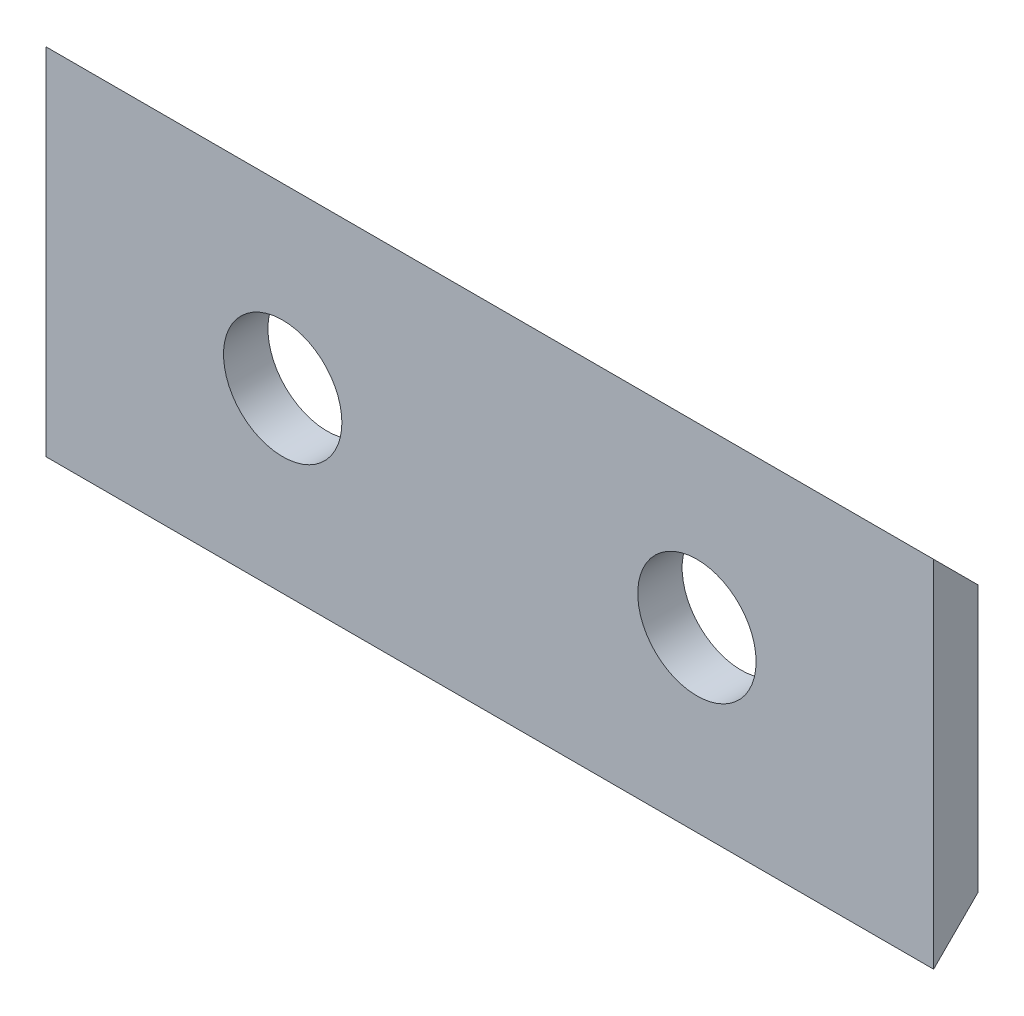
SolidWorks part; units mm, degrees
ref_plane "Front Plane" through (0, 0, 0) normal (0, 0, 1) x (1, 0, 0)
ref_plane "Top Plane" through (0, 0, 0) normal (0, 1, 0) x (1, 0, 0)
ref_plane "Right Plane" through (0, 0, 0) normal (1, 0, 0) x (0, 0, -1)
sketch "Sketch1" plane through (0, 0, 0) normal (0, 0, 1) x (1, 0, 0)
  line L1 (0, 0) -> (-30, 0)
  line L2 (0, 0) -> (0, 12)
  line L3 (0, 12) -> (-30, 12)
  line L4 (-30, 0) -> (-30, 12)
  circle A0 centre (-22, 6) radius 2
  circle A1 centre (-8, 6) radius 2
  dimension "D3" = 4
  dimension "D4" = 4
  dimension "D6" = 14
  dimension "D7" = 8
  dimension "D1" = 30
  dimension "D2" = 12
  dimension "D5" = 6
extrude "Boss-Extrude1" add sketch "Sketch1" along normal blind 1.5
sketch "Sketch2" plane through (0, 0, 0) normal (1, 0, 0) x (0, 0, -1)
  line L0 (0, 12) -> (-1.5, 12)
  line L1 (-1.5, 12) -> (0, 10.5)
  line L2 (0, 0) -> (0, 12) construction
  line L3 (0, 10.5) -> (0, 12)
  line L4 (0, 0) -> (0, 1.5)
  line L5 (0, 1.5) -> (-1.5, 0)
  line L6 (-1.5, 0) -> (0, 0)
  dimension "D1" = 45
  dimension "D2" = 45
extrude "Cut-Extrude1" cut sketch "Sketch2" against normal through all
sketch "Sketch3" plane through (0, 0, 0) normal (0, 1, 0) x (1, 0, 0)
  line L0 (0, -1.5) -> (-1.5, 0)
  line L1 (-1.5, 0) -> (0, 0)
  line L2 (0, 0) -> (0, -1.5)
  line L3 (-30, 0) -> (-30, -1.5)
  line L5 (-30, -1.5) -> (-28.5, 0)
  line L6 (-28.5, 0) -> (-30, 0)
  dimension "D1" = 45
  dimension "D2" = 45
extrude "Cut-Extrude2" [suppressed] cut sketch "Sketch3" along normal through all
